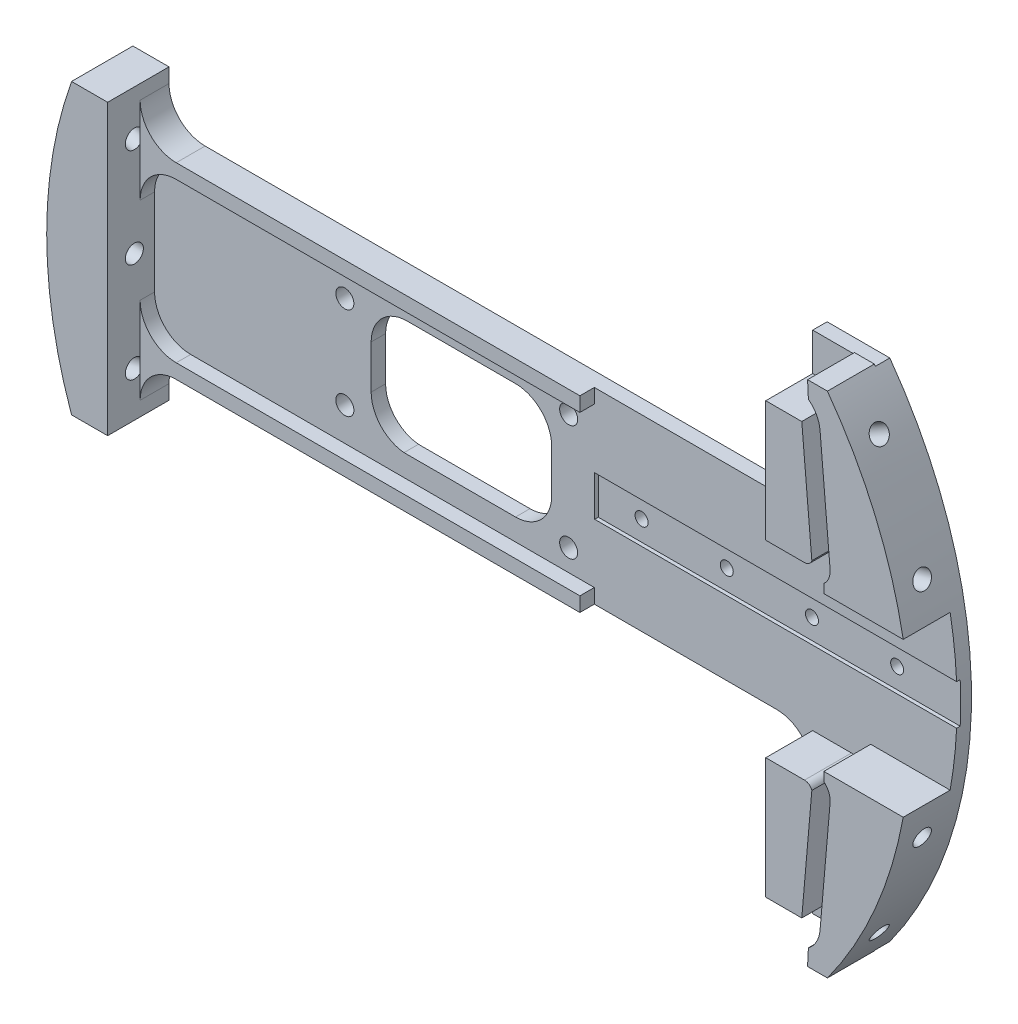
SolidWorks part; units mm, degrees
ref_plane "Front Plane" through (0, 0, 0) normal (0, 0, 1) x (1, 0, 0)
ref_plane "Top Plane" through (0, 0, 0) normal (0, 1, 0) x (1, 0, 0)
ref_plane "Right Plane" through (0, 0, 0) normal (1, 0, 0) x (0, 0, -1)
sketch "Sketch1" plane through (0, 0, 0) normal (0, 0, 1) x (1, 0, 0)
  line L0 (0, 0) -> (91.8237, 0) construction
  line L2 (-71.5726, 25.4) -> (-65.2226, 25.4)
  line L3 (50.546, 44.45) -> (50.546, 22.86)
  line L4 (50.546, -44.45) -> (50.546, -22.86)
  line L5 (44.196, -16.51) -> (-58.8726, -16.51)
  line L6 (50.546, 44.45) -> (61.5792, 44.45)
  line L7 (50.546, -44.45) -> (61.5792, -44.45)
  line L8 (-65.2226, -22.86) -> (-65.2226, -25.4)
  line L9 (44.196, 16.51) -> (-58.8726, 16.51)
  line L10 (-65.2226, 22.86) -> (-65.2226, 25.4)
  line L11 (-71.5726, -25.4) -> (-65.2226, -25.4)
  arc A0 (61.5792, -44.45) -> (61.5792, 44.45) centre (0, 0) ccw
  circle A1 centre (0, 0) radius 75.946 construction
  arc A2 (-71.5726, 25.4) -> (-71.5726, -25.4) centre (0, 0) ccw
  circle A3 centre (-31.75, 8.128) radius 1.5875
  circle A4 centre (-31.75, -8.128) radius 1.5875
  arc A5 (50.546, 22.86) -> (44.196, 16.51) centre (44.196, 22.86) cw
  arc A6 (-58.8726, 16.51) -> (-65.2226, 22.86) centre (-58.8726, 22.86) cw
  arc A7 (50.546, -22.86) -> (44.196, -16.51) centre (44.196, -22.86) ccw
  arc A8 (-58.8726, -16.51) -> (-65.2226, -22.86) centre (-58.8726, -22.86) ccw
  point P6 (75.946, 0)
  point P17 (0, 0)
  point P30 (50.546, -16.51)
  point P33 (-65.2226, -16.51)
  dimension "D1" = 75.946
  dimension "D8" = 151.892
  dimension "D11" = 75.946
  dimension "D13" = 6.35
  dimension "D7" = 3.175
  dimension ".125" = 3.175
  dimension "D2" = 27.94
  dimension "D3" = 6.35
  dimension "D4" = 11.0332
  dimension "D5" = 50.8
  dimension "D6" = 88.9
  dimension "D9" = 8.382
  dimension "D10" = 8.382
  dimension "D14" = 31.75
  dimension "1.8" = 31.75
extrude "Boss-Extrude1" add sketch "Sketch1" along normal blind 2.54
sketch "Sketch2" plane through (0, 0, 2.54) normal (0, 0, 1) x (1, 0, 0)
  line L0 (60.2463, 17.78) -> (56.2059, 64.1603) construction
  line L1 (-13.9228, 0) -> (116.9939, 0) construction
  line L2 (35.7924, 17.78) -> (109.7023, 17.78) construction
  line L3 (61.8653, 17.78) -> (60.0951, 38.1)
  line L4 (58.6516, 17.5) -> (56.8815, 37.82)
  line L5 (56.8815, 37.82) -> (50.546, 37.82)
  line L6 (58.0471, 41.7789) -> (57.9008, 44.704)
  line L7 (57.9008, 44.704) -> (61.395, 44.704)
  line L8 (50.546, 37.82) -> (50.546, 16.5667)
  line L9 (50.546, 16.5667) -> (57.3661, 16.5667)
  line L10 (60.7595, 15.0941) -> (60.7595, 13.5449)
  line L11 (60.7595, 13.5449) -> (74.7284, 13.5449)
  line L12 (60.2463, -17.78) -> (56.2059, -64.1603) construction
  line L13 (60.7595, -13.5449) -> (74.7284, -13.5449)
  line L14 (60.7595, -15.0941) -> (60.7595, -13.5449)
  line L15 (50.546, -16.5667) -> (57.3661, -16.5667)
  line L16 (50.546, -37.82) -> (50.546, -16.5667)
  line L17 (57.9008, -44.704) -> (61.395, -44.704)
  line L18 (58.0471, -41.7789) -> (57.9008, -44.704)
  line L19 (56.8815, -37.82) -> (50.546, -37.82)
  line L20 (58.6516, -17.5) -> (56.8815, -37.82)
  line L21 (61.8653, -17.78) -> (60.0951, -38.1)
  line L22 (96.3863, 0) -> (96.3863, 82.276) construction
  arc A0 (61.5792, -44.45) -> (61.5792, 44.45) centre (0, 0) ccw construction
  arc A1 (60.0951, 38.1) -> (58.0471, 41.7789) centre (54.9639, 37.653) ccw
  arc A2 (57.3661, 16.5667) -> (58.6516, 17.5) centre (57.3661, 17.9187) ccw
  arc A3 (61.8653, 17.78) -> (60.7595, 15.0941) centre (58.7167, 17.5057) cw
  arc A4 (74.7284, 13.5449) -> (61.395, 44.704) centre (0, 0) ccw
  arc A5 (74.7284, -13.5449) -> (61.395, -44.704) centre (0, 0) cw
  arc A6 (61.8653, -17.78) -> (60.7595, -15.0941) centre (58.7167, -17.5057) ccw
  arc A7 (57.3661, -16.5667) -> (58.6516, -17.5) centre (57.3661, -17.9187) cw
  arc A8 (60.0951, -38.1) -> (58.0471, -41.7789) centre (54.9639, -37.653) cw
  point P0 (75.946, 0)
  point P1 (60.2463, 17.78)
  point P49 (96.3863, 44.704)
  dimension "D6" = 75.946
  dimension "D1" = 17.78
  dimension "D2" = 15.6997
  dimension "D3" = 85.021
  dimension "D4" = 1.6129
  dimension "D5" = 20.32
  dimension "D7" = 44.704
  dimension "D8" = 44.704
  dimension "D9" = 25.4
extrude "Boss-Extrude2" add sketch "Sketch2" along normal blind 8.255
sketch "Sketch3" plane through (0, 0, 2.54) normal (0, 0, 1) x (1, 0, 0)
  line L0 (-6.3906, 0) -> (92.2963, 0) construction
  line L1 (50.546, 44.45) -> (50.546, 22.86) construction
  line L2 (12.192, -3.55) -> (76.962, -3.55)
  line L3 (12.192, -3.55) -> (12.192, 3.55)
  line L4 (12.192, 3.55) -> (76.962, 3.55)
  line L5 (76.962, -3.55) -> (76.962, 3.55)
  line L6 (12.192, -3.55) -> (76.962, 3.55) construction
  line L7 (12.192, 3.55) -> (76.962, -3.55) construction
  point P3 (44.577, 0)
  dimension "D1" = 7.1
  dimension "D2" = 64.77
  dimension "D3" = 38.354
extrude "Cut-Extrude1" cut sketch "Sketch3" against normal blind 0.635
sketch "Sketch6" plane through (0, 0, 0) normal (0, 0, -1) x (-1, 0, 0)
  line L1 (102.4877, 0) -> (-122.8054, 0) construction
sketch "Sketch7" plane through (0, 0, 0) normal (0, 0, 1) x (1, 0, 0)
  line L0 (0, 0) -> (107.1474, 0) construction
  line L1 (0, 0) -> (65.9911, 38.1) construction
  dimension "D1" = 30
ref_plane "Plane2" through (65.7712, 37.973, 0) normal (0.866, 0.5, 0) x (0, 0, -1)
sketch "Sketch9" plane through (0, 0, 2.54) normal (0, 0, 1) x (1, 0, 0)
  line L0 (-35.0108, 0) -> (91.9546, 0) construction
  circle A0 centre (7.62, -10.16) radius 1.5875
  circle A1 centre (-31.75, 8.128) radius 1.5875 construction
  circle A4 centre (7.62, 10.16) radius 1.5875
  point P9 (74.93, 0)
  dimension "D6" = 3.175
  dimension "D1" = 39.37
  dimension "D4" = 74.93
  dimension "D7" = 10.16
extrude "Cut-Extrude4" cut sketch "Sketch9" against normal through all
sketch "Sketch4" plane through (0, 0, 1.905) normal (0, 0, 1) x (1, 0, 0)
  line L0 (12.192, 3.55) -> (12.192, -3.55) construction
  line L1 (-1.4827, 0) -> (103.4049, 0) construction
  circle A0 centre (19.812, 0) radius 1.143
  circle A1 centre (34.798, 0) radius 1.143
  circle A2 centre (49.784, 0) radius 1.143
  circle A3 centre (64.77, 0) radius 1.143
  point P2 (12.192, 0)
  dimension "D2" = 2.286
  dimension "D4" = 14.986
  dimension "D1" = 7.62
  dimension "D5" = 19.812
  dimension "D3" = 4
extrude "Cut-Extrude2" cut sketch "Sketch4" against normal blind 11.43
sketch "Sketch19" plane through (0, 0, 2.54) normal (0, 0, 1) x (1, 0, 0)
  line L0 (-71.5726, -25.4) -> (-65.2226, -25.4) construction
  line L3 (-71.5726, -25.4) -> (-65.2226, -25.4)
  line L4 (-65.2226, -25.4) -> (-65.2226, 25.4)
  line L5 (-65.2226, 25.4) -> (-71.5726, 25.4) construction
  line L6 (-65.2226, 25.4) -> (-71.5726, 25.4)
  circle A0 centre (0, 0) radius 75.946 construction
  arc A3 (-71.5726, 25.4) -> (-71.5726, -25.4) centre (0, 0) ccw
  point P0 (-65.2226, -25.4)
  point P6 (-71.5726, -25.4)
  dimension "D2" = 151.892
  dimension "D1" = 6.35
extrude "Boss-Extrude5" add sketch "Sketch19" along normal blind 8.255
ref_plane "Plane3" through (0, 0, 10.795) normal (0, 0, 1) x (1, 0, 0)
sketch "Sketch22" plane through (0, 0, 10.795) normal (0, 0, 1) x (1, 0, 0)
  line L1 (-75.946, -44.45) -> (75.946, -44.45) construction
  line L2 (-75.946, -44.45) -> (-75.946, 44.45) construction
  line L3 (-75.946, 44.45) -> (75.946, 44.45) construction
  line L4 (75.946, -44.45) -> (75.946, 44.45) construction
  line L5 (-75.946, -44.45) -> (75.946, 44.45) construction
  line L6 (-75.946, 44.45) -> (75.946, -44.45) construction
  point P0 (0, 0)
  dimension "D1" = 88.9
  dimension "D2" = 151.892
sketch "Sketch24" plane through (65.7712, 37.973, 0) normal (0.866, 0.5, 0) x (0, 0, -1)
  line L0 (0, -69.2844) -> (0, 7.7053) construction
  circle A0 centre (-6.0325, -2.2244) radius 1.6383
  dimension "D1" = 3.2766
  dimension "D2" = 6.0325
sketch "Sketch25" plane through (0, 0, 0) normal (0, 0, 1) x (1, 0, 0)
  line L0 (0, 0) -> (145.0129, 0) construction
  line L1 (0, 0) -> (140.0717, -37.5321) construction
  line L2 (0, 0) -> (125.5848, -72.5064) construction
  circle A0 centre (0, 0) radius 76.2 construction
  point P9 (0, 0)
  dimension "D1" = 152.4
  dimension "D2" = 3
ref_plane "Plane4" through (0, 0, 6.096) normal (0, 0, 1) x (1, 0, 0)
sketch "Sketch27" plane through (0, 0, 6.096) normal (0, 0, 1) x (1, 0, 0)
  line L0 (-98.5098, 0) -> (76.2, 0) construction
  line L1 (0, 0) -> (143.2275, -38.3777) construction
  line L2 (0, 0) -> (128.4143, -74.14) construction
  line L3 (0, 0) -> (143.2275, 38.3777) construction
  line L4 (0, 0) -> (128.4143, 74.14) construction
  line L5 (-95.1532, 25.4962) -> (73.6035, -19.722) construction
  line L6 (-95.1532, -25.4962) -> (73.6035, 19.722) construction
  circle A0 centre (0, 0) radius 76.2 construction
  point P5 (3.2671, -47.4697)
  point P10 (0, 0)
  point P13 (0, 0)
  point P17 (0, 0)
  point P19 (0, 0)
  dimension "D1" = 3
  dimension "D2" = 3
  dimension "D3" = 2
  dimension "D4" = 2
ref_plane "Plane5" through (65.7712, 37.973, 0) normal (0.866, 0.5, 0) x (0, 0, -1)
sketch "Sketch28" plane through (65.7712, 37.973, 0) normal (0.866, 0.5, 0) x (0, 0, -1)
  line L0 (0, -69.2844) -> (0, 7.7053) construction
  line L1 (-10.795, 8.0173) -> (-2.54, 8.0173) construction
  circle A0 centre (-6.0533, 0) radius 1.5875
  dimension "D1" = 3.175
  dimension "D2" = 6.0533
  dimension "D3" = 8.0173
extrude "Cut-Extrude12" cut sketch "Sketch28" against normal blind 7.62 contours A0
ref_plane "Plane6" through (73.3582, 19.6563, 0) normal (0.9659, 0.2588, 0) x (0, 0, -1)
ref_plane "Plane7" through (73.3582, -19.6563, 0) normal (0.9659, -0.2588, 0) x (0, 0, -1)
ref_plane "Plane8" through (65.7712, -37.973, 0) normal (0.866, -0.5, 0) x (0, 0, -1)
sketch "Sketch29" plane through (73.3582, 19.6563, 0) normal (0.9659, 0.2588, 0) x (0, 0, -1)
  circle A0 centre (-6.096, 0) radius 1.5875
  dimension "D1" = 3.175
extrude "Cut-Extrude13" cut sketch "Sketch29" against normal blind 10.16
ref_plane "Plane9" through (0, 0, 0) normal (0, 1, 0) x (1, 0, 0)
mirror "Mirror3" about plane through (0, 0, 0) normal (0, 1, 0) of "Cut-Extrude12", "Cut-Extrude13"
ref_plane "Plane10" through (-73.3582, 19.6563, 0) normal (-0.9659, 0.2588, 0) x (0, 0, 1)
ref_plane "Plane11" through (-75.946, 0, 0) normal (-1, 0, 0) x (0, 0, 1)
ref_plane "Plane12" through (-73.3582, -19.6563, 0) normal (-0.9659, -0.2588, 0) x (0, 0, 1)
sketch "Sketch30" plane through (-73.3582, 19.6563, 0) normal (-0.9659, 0.2588, 0) x (0, 0, 1)
  circle A0 centre (6.096, 0) radius 1.5875
  dimension "D1" = 3.175
extrude "Cut-Extrude14" cut sketch "Sketch30" against normal blind 12.7 contours A0
sketch "Sketch31" plane through (-75.946, 0, 0) normal (-1, 0, 0) x (0, 0, 1)
  circle A0 centre (6.096, 0) radius 1.5875
  dimension "D1" = 3.175
extrude "Cut-Extrude15" cut sketch "Sketch31" against normal blind 12.7
sketch "Sketch32" plane through (-73.3582, -19.6563, 0) normal (-0.9659, -0.2588, 0) x (0, 0, 1)
  circle A0 centre (6.096, 0) radius 1.5875
  dimension "D1" = 3.175
extrude "Cut-Extrude16" cut sketch "Sketch32" against normal blind 12.7
sketch "Sketch33" plane through (0, 0, 2.54) normal (0, 0, 1) x (1, 0, 0)
  line L0 (44.196, 16.51) -> (-58.8726, 16.51) construction
  line L1 (12.1373, 16.51) -> (-58.8726, 16.51)
  line L2 (44.196, 15.24) -> (-58.8726, 15.24) construction
  line L3 (12.1373, 13.97) -> (-58.8726, 13.97)
  line L4 (0, 0) -> (-34.589, 0) construction
  line L5 (-65.2226, 22.86) -> (-65.2226, 7.62)
  line L6 (12.1373, 13.97) -> (12.1373, 16.51)
  line L7 (12.1373, -13.97) -> (12.1373, -16.51)
  line L8 (44.196, 16.51) -> (-58.8726, 16.51) construction
  line L9 (44.196, -15.24) -> (-58.8726, -15.24) construction
  line L10 (12.1373, -16.51) -> (-58.8726, -16.51)
  line L11 (12.1373, -13.97) -> (-58.8726, -13.97)
  line L12 (-65.2226, -22.86) -> (-65.2226, -7.62)
  arc A0 (-65.2226, 22.86) -> (-58.8726, 16.51) centre (-58.8726, 22.86) ccw construction
  arc A1 (-65.2226, 22.86) -> (-58.8726, 16.51) centre (-58.8726, 22.86) ccw
  arc A2 (-65.2226, 7.62) -> (-58.8726, 13.97) centre (-58.8726, 7.62) cw
  arc A3 (-66.4926, 22.86) -> (-58.8726, 15.24) centre (-58.8726, 22.86) ccw construction
  arc A4 (-65.2226, -7.62) -> (-58.8726, -13.97) centre (-58.8726, -7.62) ccw
  arc A5 (-65.2226, -22.86) -> (-58.8726, -16.51) centre (-58.8726, -22.86) cw
  dimension "D2" = 71.0099
  dimension "D3" = 2.54
  dimension "D1" = 1.27
extrude "Boss-Extrude6" add sketch "Sketch33" along normal blind 2.54
sketch "Sketch34" plane through (0, 0, 2.54) normal (0, 0, 1) x (1, 0, 0)
  line L1 (-20.7726, 10.16) -> (-1.7226, 10.16)
  line L2 (-27.1226, -3.8353) -> (-27.1226, 3.81)
  line L3 (-1.7226, -10.16) -> (-21.3391, -10.16)
  line L4 (-58.8726, 13.97) -> (12.1373, 13.97) construction
  line L6 (-65.2226, -7.62) -> (-65.2226, 7.62) construction
  line L11 (4.6274, 3.81) -> (4.6274, -3.81)
  arc A2 (-21.3391, -10.16) -> (-27.1226, -3.8353) centre (-20.7726, -3.8353) cw
  arc A3 (-20.7726, 10.16) -> (-27.1226, 3.81) centre (-20.7726, 3.81) ccw
  arc A5 (4.6274, -3.81) -> (-1.7226, -10.16) centre (-1.7226, -3.81) cw
  arc A6 (4.6274, 3.81) -> (-1.7226, 10.16) centre (-1.7226, 3.81) ccw
  dimension "D3" = 6.35
  dimension "D8" = 7.62
  dimension "D6" = 6.35
  dimension "D7" = 7.6453
  dimension "D1" = 20.32
  dimension "D2" = 31.75
  dimension "D4" = 3.81
  dimension "D5" = 38.1
extrude "Cut-Extrude17" cut sketch "Sketch34" against normal through all
equation "\"0.15inin\"=0.2"
equation "\"0.45inin\"=0.35"
equation "\"0.55inin\"=0.45"
equation "\"0.125inin\"=0.325"
